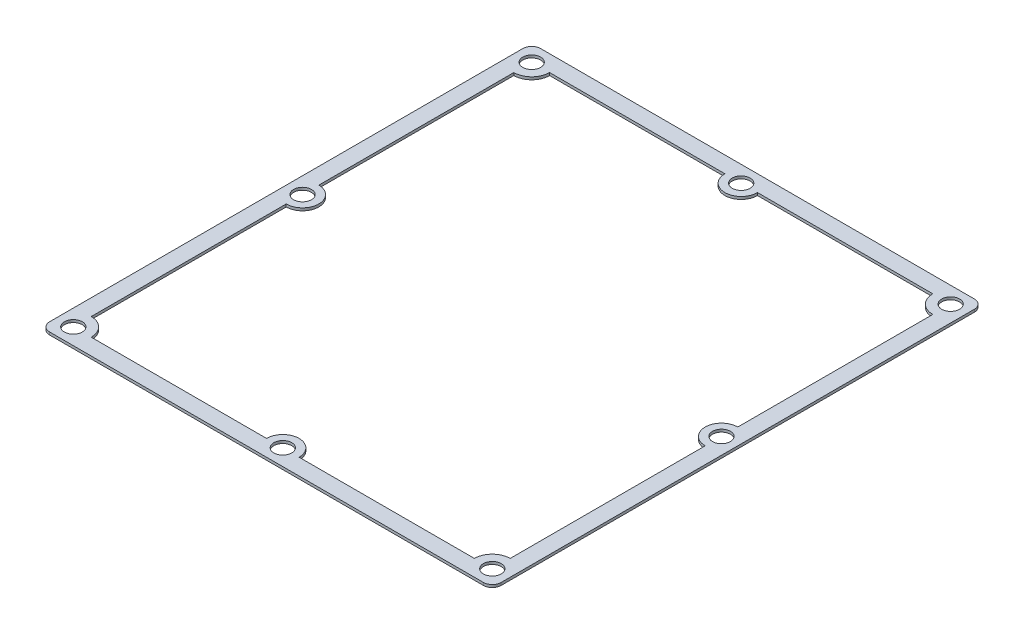
SolidWorks part; units mm, degrees
ref_plane "Спереди" through (0, 0, 0) normal (0, 0, 1) x (1, 0, 0)
ref_plane "Сверху" through (0, 0, 0) normal (0, 1, 0) x (1, 0, 0)
ref_plane "Справа" through (0, 0, 0) normal (1, 0, 0) x (0, 0, -1)
sketch "Эскиз1" plane through (0, 0, 0) normal (0, 1, 0) x (1, 0, 0)
  line L0 (-40.771, -46.9112) -> (41.729, -46.9112)
  line L1 (43.429, -45.2112) -> (43.429, 44.7888)
  line L2 (-42.471, 44.7888) -> (-42.471, -45.2112)
  line L3 (41.729, 46.4888) -> (-40.771, 46.4888)
  line L4 (-39.371, 39.9873) -> (-39.371, 2.8888)
  line L5 (-35.9696, 43.3888) -> (-2.621, 43.3888)
  line L6 (0.479, 46.4888) -> (0.479, -46.9112) construction
  line L7 (-35.9696, -43.8112) -> (-2.621, -43.8112)
  line L8 (40.329, 39.9873) -> (40.329, 2.8888)
  line L9 (3.579, 43.3888) -> (36.9275, 43.3888)
  line L10 (-42.471, -0.2112) -> (43.429, -0.2112) construction
  line L11 (3.579, -43.8112) -> (36.9275, -43.8112)
  line L12 (-39.371, -3.3112) -> (-39.371, -40.4098)
  line L13 (40.329, -3.3112) -> (40.329, -40.4098)
  circle A0 centre (-39.371, -0.2112) radius 1.7
  circle A1 centre (-39.371, -43.8112) radius 1.7
  arc A2 (-42.471, -45.2112) -> (-40.771, -46.9112) centre (-40.771, -45.2112) ccw
  circle A3 centre (0.479, -43.8112) radius 1.7
  arc A4 (41.729, -46.9112) -> (43.429, -45.2112) centre (41.729, -45.2112) ccw
  circle A5 centre (40.329, -43.8112) radius 1.7
  circle A6 centre (40.329, -0.2112) radius 1.7
  arc A7 (43.429, 44.7888) -> (41.729, 46.4888) centre (41.729, 44.7888) ccw
  circle A8 centre (40.329, 43.3888) radius 1.7
  circle A9 centre (0.479, 43.3888) radius 1.7
  circle A10 centre (-39.371, 43.3888) radius 1.7
  arc A11 (-40.771, 46.4888) -> (-42.471, 44.7888) centre (-40.771, 44.7888) ccw
  arc A12 (-39.371, 39.9873) -> (-35.9696, 43.3888) centre (-39.371, 43.3888) ccw
  arc A13 (-2.621, 43.3888) -> (3.579, 43.3888) centre (0.479, 43.3888) ccw
  arc A14 (40.329, 39.9873) -> (36.9275, 43.3888) centre (40.329, 43.3888) cw
  arc A15 (40.329, -40.4098) -> (36.9275, -43.8112) centre (40.329, -43.8112) ccw
  arc A16 (-2.621, -43.8112) -> (3.579, -43.8112) centre (0.479, -43.8112) cw
  arc A17 (-39.371, -40.4098) -> (-35.9696, -43.8112) centre (-39.371, -43.8112) cw
  arc A18 (-39.371, -3.3112) -> (-39.371, 2.8888) centre (-39.371, -0.2112) ccw
  arc A19 (40.329, 2.8888) -> (40.329, -3.3112) centre (40.329, -0.2112) ccw
extrude "Бобышка-Вытянуть1" add sketch "Эскиз1" along normal blind 0.5
